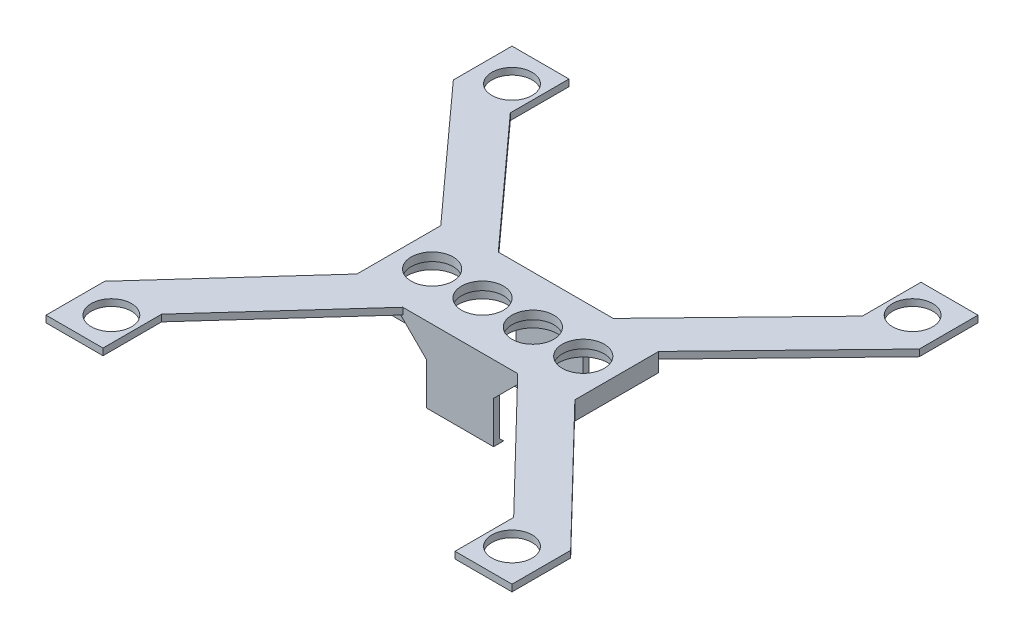
SolidWorks part; units mm, degrees
ref_plane "Přední rovina" through (0, 0, 0) normal (0, 0, 1) x (1, 0, 0)
ref_plane "Horní rovina" through (0, 0, 0) normal (0, 1, 0) x (1, 0, 0)
ref_plane "Pravá rovina" through (0, 0, 0) normal (1, 0, 0) x (0, 0, -1)
sketch "Skica1" plane through (0, 0, 0) normal (0, 0, 1) x (1, 0, 0)
  line L0 (-52.1567, -7.7147) -> (-26.1567, -7.7147)
  line L12 (-52.1567, -6.7147) -> (-26.1567, -6.7147)
  line L15 (-52.1567, -6.7147) -> (-52.1567, -7.7147)
  line L18 (-26.1567, -6.7147) -> (-26.1567, -7.7147)
  point P2 (-39.1567, -7.7147)
  dimension "D1" = 13
  dimension "D2" = 1
extrude "Přidat vysunutím1" add sketch "Skica1" along normal blind 10 contours L0 L18 L12 L15
sketch "Skica2" plane through (0, -7.7147, 0) normal (0, -1, 0) x (-1, 0, 0)
  line L0 (26.1567, -10) -> (26.1567, 0) construction
  line L1 (52.1567, -10) -> (26.1567, -10) construction
  circle A0 centre (48.1867, -5) radius 2.5
  circle A1 centre (42.1767, -5) radius 2.5
  circle A2 centre (36.1667, -5) radius 2.5
  circle A3 centre (30.1567, -5) radius 2.5
  dimension "D1" = 5
  dimension "D3" = 5
  dimension "D5" = 4
  dimension "D4" = 4
extrude "Odebrat vysunutím1" cut sketch "Skica2" against normal blind 1
sketch "Skica3" plane through (0, -6.7147, 0) normal (0, 1, 0) x (1, 0, 0)
  line L0 (-32.9567, 0) -> (-17.6567, 15.8)
  line L25 (-52.1567, 0) -> (-26.1567, 0) construction
  line L27 (-26.1567, 0) -> (-10.8567, 15.8)
  line L29 (-26.1567, 0) -> (-32.9567, 0)
  line L34 (-52.1567, 0) -> (-45.3567, 0)
  line L35 (-52.1567, 0) -> (-66.4567, 15.8)
  line L37 (-45.3567, 0) -> (-59.6567, 15.8)
  line L47 (-45.3567, -10) -> (-59.6567, -25.8)
  line L49 (-52.1567, -10) -> (-66.4567, -25.8)
  line L50 (-52.1567, -10) -> (-45.3567, -10)
  line L51 (-26.1567, -10) -> (-32.9567, -10)
  line L53 (-26.1567, -10) -> (-10.8567, -25.8)
  line L54 (-32.9567, -10) -> (-17.6567, -25.8)
  line L55 (-52.1567, -10) -> (-26.1567, -10) construction
  line L56 (-66.4567, 15.8) -> (-66.4567, 22.8)
  line L57 (-66.4567, 22.8) -> (-59.6567, 22.8)
  line L59 (-59.6567, 22.8) -> (-59.6567, 15.8)
  line L60 (-59.6567, -25.8) -> (-59.6567, -32.8)
  line L61 (-59.6567, -32.8) -> (-66.4567, -32.8)
  line L62 (-66.4567, -32.8) -> (-66.4567, -25.8)
  line L63 (-17.6567, -25.8) -> (-17.6567, -32.8)
  line L64 (-17.6567, -32.8) -> (-10.8567, -32.8)
  line L65 (-10.8567, -32.8) -> (-10.8567, -25.8)
  line L66 (-10.8567, 15.8) -> (-10.8567, 22.8)
  line L67 (-10.8567, 22.8) -> (-17.6567, 22.8)
  line L68 (-17.6567, 22.8) -> (-17.6567, 15.8)
  circle A0 centre (-62.5567, 18.9) radius 2.4
  circle A1 centre (-14.7567, 18.9) radius 2.4
  circle A2 centre (-62.5567, -28.9) radius 2.4
  circle A3 centre (-14.7567, -28.9) radius 2.4
  dimension "D7" = 6.8
  dimension "D9" = 4.8
  dimension "D14" = 4.8
  dimension "D18" = 4.8
  dimension "D31" = 4.8
  dimension "D3" = 7
  dimension "D4" = 22.8
  dimension "D10" = 6.8
  dimension "D11" = 0
  dimension "D12" = 3.9
  dimension "D13" = 3.9
  dimension "D15" = 7
  dimension "D16" = 0
  dimension "D17" = 3.9
  dimension "D19" = 3.9
  dimension "D20" = 3.9
  dimension "D21" = 6.8
  dimension "D22" = 6.8
  dimension "D23" = 6.8
  dimension "D24" = 0
  dimension "D25" = 6.8
  dimension "D26" = 55.6
  dimension "D27" = 55.6
  dimension "D28" = 6.8
  dimension "D29" = 55.6
  dimension "D30" = 55.6
  dimension "D32" = 3.9
  dimension "D33" = 6.8
  dimension "D34" = 3.9
  dimension "D35" = 3.9
  dimension "D36" = 22.8
  dimension "D37" = 22.8
  dimension "D38" = 10
  dimension "D39" = 10
extrude "Přidat vysunutím2" add sketch "Skica3" against normal blind 0.8
sketch "Skica4" plane through (0, -7.7147, 0) normal (0, -1, 0) x (-1, 0, 0)
  line L1 (52.1567, -10) -> (26.1567, -10)
  line L2 (52.1567, -10) -> (52.1567, 0)
  line L3 (52.1567, 0) -> (26.1567, 0)
  line L4 (26.1567, -10) -> (26.1567, 0)
  circle A0 centre (48.1867, -5) radius 3
  circle A1 centre (42.1767, -5) radius 3
  circle A2 centre (36.1667, -5) radius 3
  circle A3 centre (30.1567, -5) radius 3
  dimension "D1" = 6
  dimension "D2" = 6
  dimension "D3" = 6
  dimension "D4" = 6
extrude "Přidat vysunutím3" add sketch "Skica4" along normal blind 1.2
sketch "Skica6" plane through (0, -6.7147, 0) normal (0, 1, 0) x (1, 0, 0)
  line L0 (-45.3567, 0) -> (-32.9567, 0) construction
  line L1 (-43.1567, 0) -> (-35.1567, 0)
  line L2 (-43.1567, 0) -> (-43.1567, 0.7)
  line L3 (-43.1567, 0.7) -> (-35.1567, 0.7)
  line L4 (-35.1567, 0) -> (-35.1567, 0.7)
  line L5 (-45.3567, -10) -> (-32.9567, -10) construction
  line L6 (-43.1567, -10) -> (-35.1567, -10)
  line L7 (-43.1567, -10) -> (-43.1567, -10.7)
  line L8 (-43.1567, -10.7) -> (-35.1567, -10.7)
  line L9 (-35.1567, -10) -> (-35.1567, -10.7)
  dimension "D1" = 0.7
  dimension "D2" = 8
  dimension "D3" = 2.2
  dimension "D4" = 2.2
  dimension "D5" = 0.7
extrude "Přidat vysunutím5" add sketch "Skica6" against normal blind 9
sketch "Skica7" plane through (-35.1567, 0, 0) normal (1, 0, 0) x (0, 0, -1)
  line L9 (-10, -15.7147) -> (-9.5, -15.7147)
  line L10 (-9.5, -15.7147) -> (-10, -15.2147)
  line L11 (-10, -15.7147) -> (-10, -8.9147) construction
  line L12 (-10, -15.2147) -> (-10, -15.7147)
  line L13 (0, -15.7147) -> (0, -15.2147)
  line L14 (0, -15.7147) -> (0, -8.9147) construction
  line L15 (0, -15.2147) -> (-0.5, -15.7147)
  line L16 (-0.5, -15.7147) -> (0, -15.7147)
  dimension "D1" = 0.5
  dimension "D2" = 0.5
  dimension "D3" = 0.5
extrude "Přidat vysunutím6" add sketch "Skica7" against normal blind 8
sketch "Skica8" plane through (0, 0, 0) normal (0, 0, -1) x (-1, 0, 0)
  line L0 (43.1567, -6.7147) -> (43.1567, -10.7147)
  line L1 (43.1567, -15.2147) -> (43.1567, -8.9147) construction
  line L2 (43.1567, -6.7147) -> (47.1567, -6.7147)
  line L3 (47.1567, -6.7147) -> (43.1567, -10.7147)
  line L4 (35.1567, -10.7147) -> (35.1567, -6.7147)
  line L5 (35.1567, -15.2147) -> (35.1567, -8.9147) construction
  line L6 (35.1567, -6.7147) -> (31.1567, -6.7147)
  line L7 (31.1567, -6.7147) -> (35.1567, -10.7147)
  dimension "D1" = 4
  dimension "D2" = 4
  dimension "D3" = 4
extrude "Přidat vysunutím8" add sketch "Skica8" along normal blind 0.7
sketch "Skica9" plane through (0, 0, 10) normal (0, 0, 1) x (1, 0, 0)
  line L0 (-43.1567, -6.7147) -> (-47.1567, -6.7147)
  line L1 (-59.6567, -6.7147) -> (-45.3567, -6.7147) construction
  line L2 (-43.1567, -6.7147) -> (-43.1567, -10.7147)
  line L3 (-43.1567, -15.7147) -> (-43.1567, -6.7147) construction
  line L4 (-43.1567, -10.7147) -> (-47.1567, -6.7147)
  line L5 (-35.1567, -6.7147) -> (-35.1567, -10.7147)
  line L6 (-35.1567, -15.2147) -> (-35.1567, -8.9147) construction
  line L7 (-35.1567, -10.7147) -> (-31.1567, -6.7147)
  line L8 (-31.1567, -6.7147) -> (-35.1567, -6.7147)
  dimension "D1" = 4
  dimension "D2" = 4
extrude "Přidat vysunutím9" add sketch "Skica9" along normal blind 0.7
